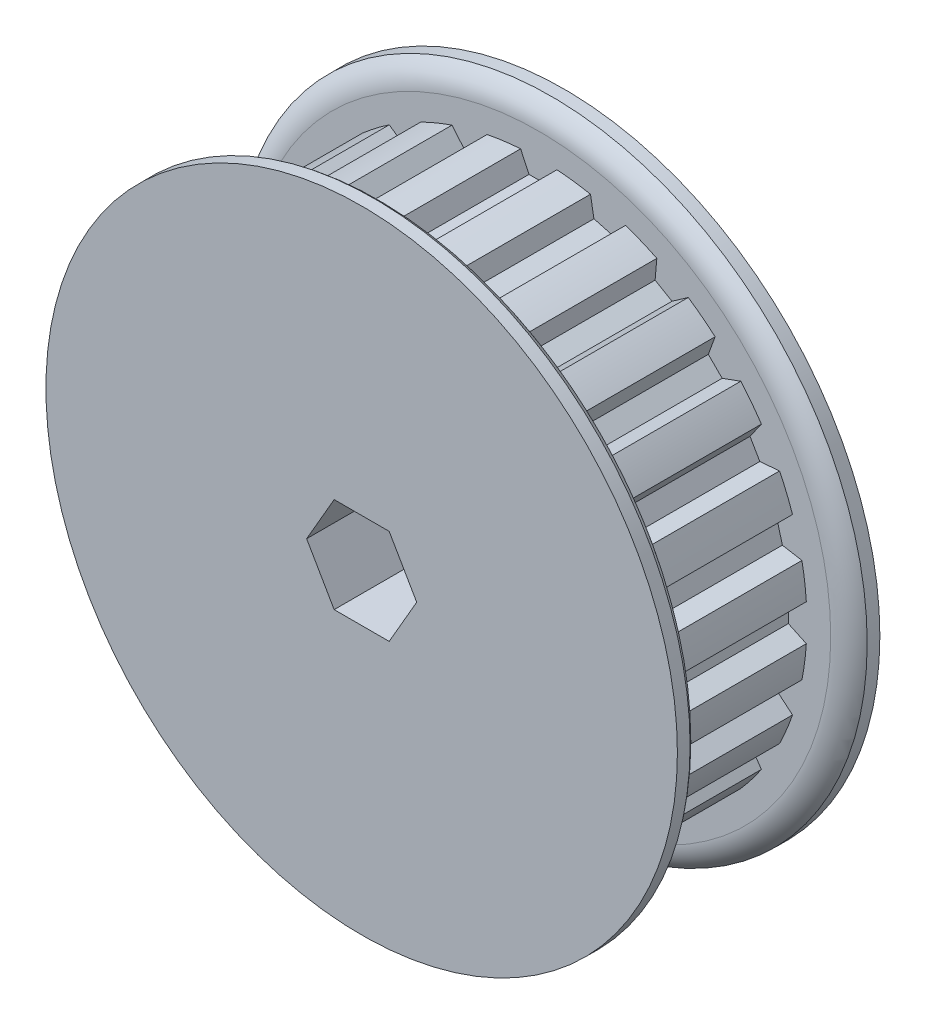
SolidWorks part; units mm, degrees
ref_plane "Front Plane" through (0, 0, 0) normal (0, 0, 1) x (1, 0, 0)
ref_plane "Top Plane" through (0, 0, 0) normal (0, 1, 0) x (1, 0, 0)
ref_plane "Right Plane" through (0, 0, 0) normal (1, 0, 0) x (0, 0, -1)
sketch "Sketch1" plane through (0, 0, 0) normal (0, 0, 1) x (1, 0, 0)
  line L0 (-1.2827, 18.8976) -> (-0.6905, 17.6276)
  line L1 (-0.6905, 17.6276) -> (0.6905, 17.6276)
  line L2 (0.6905, 17.6276) -> (1.2827, 18.8976)
  line L3 (-1.2827, 18.8976) -> (1.2827, 18.8976)
  line L4 (0, 0) -> (0, 17.6276) construction
  line L5 (0, 17.6276) -> (0, 19.9136) construction
  circle A0 centre (0, 0) radius 19.4056 construction
  circle A1 centre (0, 0) radius 22.3012 construction
  circle A2 centre (0, 0) radius 18.9411 construction
  point P6 (0, 18.8976)
  point P11 (0, 19.4056)
  point P13 (0, 22.3012)
  point P14 (0, 18.9411)
  dimension "D1" = 1.016
  dimension "D2" = 0.508
sketch "Sketch2" plane through (0, 0, 0) normal (1, 0, 0) x (0, 0, -1)
  line L0 (-11.1125, 3.175) -> (11.1125, 3.175)
  line L1 (-11.1125, 3.175) -> (-11.1125, 13.5001)
  line L2 (-11.1125, 13.5001) -> (-3.1877, 13.5001)
  line L3 (-3.1877, 13.5001) -> (-3.1877, 22.3012)
  line L4 (-3.1877, 22.3012) -> (-1.397, 22.3012) construction
  line L5 (-1.397, 22.3012) -> (-1.397, 18.9411) construction
  line L6 (-1.397, 18.9411) -> (9.3218, 18.9411)
  line L7 (9.3218, 18.9411) -> (9.3218, 22.3012) construction
  line L8 (9.3218, 22.3012) -> (11.1125, 22.3012) construction
  line L9 (11.1125, 22.3012) -> (11.1125, 3.175)
  line L10 (-11.1125, 0) -> (11.1125, 0) construction
  line L13 (-3.1877, 22.3012) -> (-2.2923, 22.3012)
  line L14 (-1.397, 20.6211) -> (-1.397, 18.9411)
  line L15 (9.3218, 18.9411) -> (9.3218, 20.6211)
  line L16 (10.2172, 22.3012) -> (11.1125, 22.3012)
  arc A0 (-1.397, 20.6211) -> (-2.2923, 22.3012) centre (-3.4209, 20.6211) ccw
  arc A1 (9.3218, 20.6211) -> (10.2172, 22.3012) centre (11.3457, 20.6211) cw
  point P12 (-1.397, 20.6211)
  point P14 (-2.2923, 22.3012)
  point P20 (9.3218, 20.6211)
  point P21 (10.2172, 22.3012)
  point P25 (9.3218, 0)
  point P26 (-1.397, 0)
  dimension "Bore" = 6.35
  dimension "Hub Dia" = 27.0002
  dimension "Outside Width" = 14.3002
  dimension "Inside Width" = 10.7188
revolve "Revolve1" add sketch "Sketch2" angle 360 mid plane about L10
sketch "Sketch3" plane through (0, 0, 0) normal (0, 0, 1) x (1, 0, 0)
  line L0 (-0.6905, 17.6276) -> (0.6905, 17.6276) construction
  line L1 (0.6905, 17.6276) -> (1.2827, 18.8976) construction
  line L2 (-1.2827, 18.8976) -> (-0.6905, 17.6276) construction
  line L3 (-0.6905, 17.6276) -> (0.6905, 17.6276)
  line L4 (0.6905, 17.6276) -> (1.2827, 18.8976)
  line L5 (-1.2827, 18.8976) -> (-0.6905, 17.6276)
  circle A0 centre (0, 0) radius 18.9411 construction
  arc A1 (1.2827, 18.8976) -> (-1.2827, 18.8976) centre (0, 0) ccw
extrude "Cut-Extrude1" cut sketch "Sketch3" against normal up to vertex (9.3218 mm away) from vertex at 1.397 starting at point (0, 18.9411, 1.397)
pattern_circular "CirPattern1" count 24 over 360 about axis through (0, 0, 0) along (0, 0, 1) of "Cut-Extrude1"
sketch "Sketch4" plane through (0, 0, 0) normal (0, 1, 0) x (1, 0, 0)
  line L0 (0, -3.1877) -> (0, -11.1125) construction
  line L1 (-13.5001, -3.1877) -> (13.5001, -3.1877) construction
  line L2 (-13.5001, -11.1125) -> (13.5001, -11.1125) construction
  circle A0 centre (0, -7.1501) radius 1.5875
  dimension "D1" = 3.175
extrude "Cut-Extrude2" cut sketch "Sketch4" along normal through all
ref_plane "Plane1" through (0, 0, 7.1501) normal (0, 0, 1) x (1, 0, 0)
sketch "Sketch5" plane through (0, 0, 7.1501) normal (0, 0, 1) x (1, 0, 0)
  line L0 (0, 0) -> (0, 13.5001) construction
  line L1 (1.0795, 13.4064) -> (1.5875, 12.8984)
  line L2 (0, 13.4064) -> (1.0795, 13.4064)
  line L3 (0, 13.4064) -> (0, 3.175)
  line L4 (0, 3.175) -> (0.9525, 3.175)
  line L5 (1.5875, 12.8984) -> (1.5875, 3.81)
  line L6 (0.9525, 3.175) -> (1.5875, 3.81)
  circle A0 centre (0, 0) radius 13.5001 construction
  circle A1 centre (0, 0) radius 3.175 construction
  point P7 (1.5875, 3.175)
  point P9 (1.5875, 13.4064)
revolve "Revolve2" add sketch "Sketch5" angle 360 mid plane about L0
sketch "Sketch6" plane through (0, 13.4064, 0) normal (0, 1, 0) x (1, 0, 0)
  line L1 (0, -6.2336) -> (-0.7938, -6.6918)
  line L2 (-0.7938, -6.6918) -> (-0.7937, -7.6084)
  line L3 (-0.7937, -7.6084) -> (0, -8.0666)
  line L4 (0, -8.0666) -> (0.7938, -7.6084)
  line L5 (0.7938, -7.6084) -> (0.7938, -6.6918)
  line L6 (0.7938, -6.6918) -> (0, -6.2336)
  circle A0 centre (0, -7.1501) radius 0.7938 construction
  dimension "D1" = 1.5875
extrude "Cut-Extrude3" cut sketch "Sketch6" against normal blind 1.1906
pattern_circular "CirPattern2" count 2 every 90 about axis through (0, 0, 0) along (0, 0, 1) of "Cut-Extrude2", "Revolve2", "Cut-Extrude3"
sketch "Sketch7" plane through (0, 0, 11.1125) normal (0, 0, 1) x (1, 0, 0)
  circle A0 centre (0, 0) radius 13.5001
  circle A1 centre (0, 0) radius 13.5001 construction
extrude "Cut-Extrude4" cut sketch "Sketch7" against normal up to surface (7.9248 mm away) up to face at (13.5001, 0, 3.1877)
sketch "Sketch8" plane through (0, 0, 3.1877) normal (0, 0, 1) x (1, 0, 0)
  line L1 (3.8861, 0) -> (1.9431, 3.3655)
  line L2 (1.9431, 3.3655) -> (-1.9431, 3.3655)
  line L3 (-1.9431, 3.3655) -> (-3.8861, 0)
  line L4 (-3.8861, 0) -> (-1.9431, -3.3655)
  line L5 (-1.9431, -3.3655) -> (1.9431, -3.3655)
  line L6 (1.9431, -3.3655) -> (3.8861, 0)
  circle A0 centre (0, 0) radius 3.3655 construction
  dimension "D1" = 6.731
extrude "Cut-Extrude5" cut sketch "Sketch8" against normal through all
equation "\"D2@Sketch1\" = \"D1@Sketch1\"/2"
equation "\"D1@Sketch4\" = \"Bore@Sketch2\"/2"
equation "\"D1@Sketch6\" = \"D1@Sketch4\"/2"
equation "\"D1@Cut-Extrude3\" = \"D1@Sketch6\"*.75"
